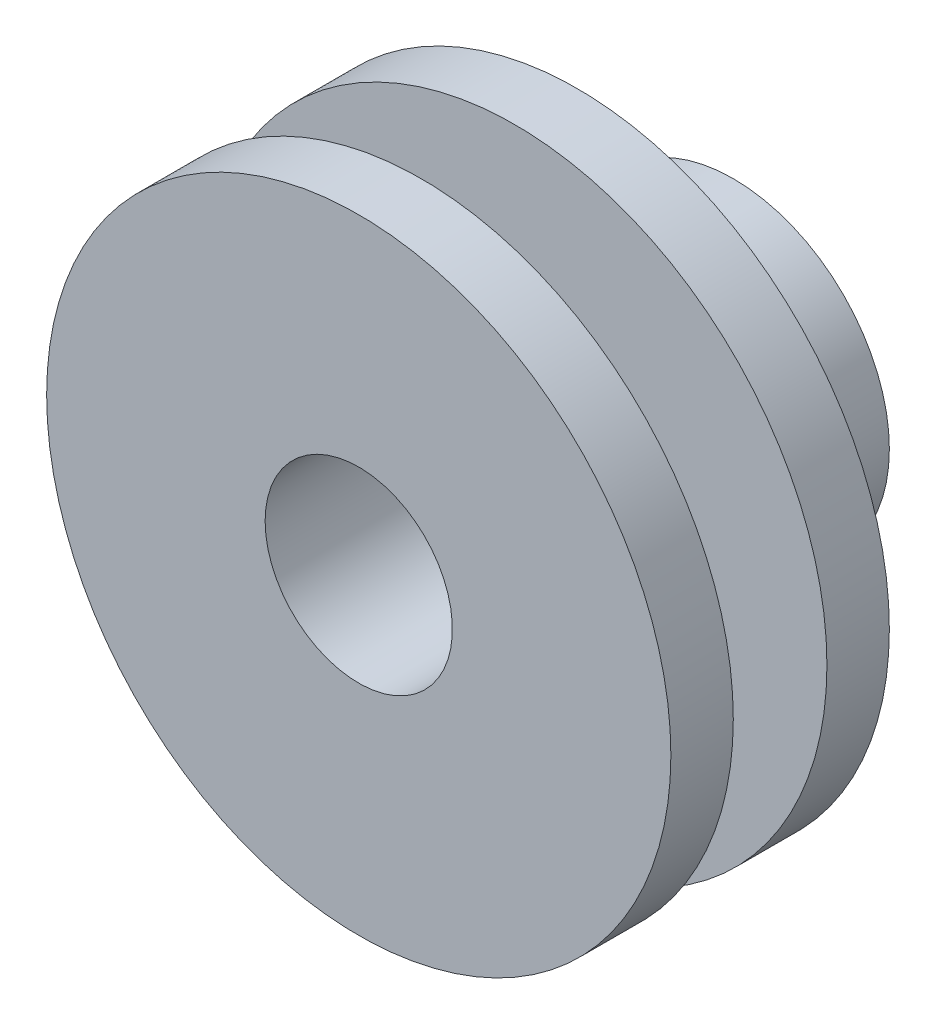
SolidWorks part; units mm, degrees
ref_plane "正面" through (0, 0, 0) normal (0, 0, 1) x (1, 0, 0)
ref_plane "平面" through (0, 0, 0) normal (0, 1, 0) x (1, 0, 0)
ref_plane "右側面" through (0, 0, 0) normal (1, 0, 0) x (0, 0, -1)
sketch "ｽｹｯﾁ1" plane through (0, 0, 0) normal (0, 0, 1) x (1, 0, 0)
  circle A0 centre (0, 0) radius 3
  circle A1 centre (0, 0) radius 5
  dimension "D1" = 6
  dimension "D2" = 10
extrude "ﾎﾞｽ - 押し出し1" add sketch "ｽｹｯﾁ1" along normal blind 5
sketch "ｽｹｯﾁ2" plane through (0, 0, 5) normal (0, 0, 1) x (1, 0, 0)
  circle A0 centre (0, 0) radius 3
  circle A1 centre (0, 0) radius 10
  dimension "D1" = 20
extrude "ﾎﾞｽ - 押し出し2" add sketch "ｽｹｯﾁ2" along normal blind 2
sketch "ｽｹｯﾁ3" plane through (0, 0, 7) normal (0, 0, 1) x (1, 0, 0)
  circle A0 centre (0, 0) radius 5
  dimension "D1" = 10
extrude "ﾎﾞｽ - 押し出し3" add sketch "ｽｹｯﾁ3" along normal blind 3
sketch "ｽｹｯﾁ4" plane through (0, 0, 10) normal (0, 0, 1) x (1, 0, 0)
  circle A0 centre (0, 0) radius 10
  dimension "D1" = 20
extrude "ﾎﾞｽ - 押し出し4" add sketch "ｽｹｯﾁ4" along normal blind 2
sketch "ｽｹｯﾁ5" plane through (0, 0, 7) normal (0, 0, -1) x (-1, 0, 0)
  circle A0 centre (0, 0) radius 3
extrude "ｶｯﾄ - 押し出し1" cut sketch "ｽｹｯﾁ5" against normal through all
hole_wizard "M3x0.5 ねじ穴1" positions "3Dｽｹｯﾁ1" profile "ｽｹｯﾁ6" tap size "M3x0.5" standard "JIS"
sketch3d "3Dｽｹｯﾁ1"
  point P0 (0.2512, -4.9937, 2.1439)
sketch "ｽｹｯﾁ6" plane through (0.2512, -4.9937, 2.1439) normal (0, 0, 1) x (0.9987, 0.0502, 0)
  line L0 (0, 0) -> (0, 2)
  line L1 (0, 2) -> (1.25, 2)
  line L2 (1.25, 2) -> (1.25, 0)
  line L5 (1.25, 0) -> (0, 0)
  line L11 (0, -6.35) -> (0, 107.95) construction
  dimension "次ｻｰﾌｪｽまでのねじ下穴ﾄﾞﾘﾙ直径" = 2.5
  dimension "次ｻｰﾌｪｽまでのねじ下穴ﾄﾞﾘﾙの深さ" = 2
cosmetic thread "穴のねじ山1" parameters "D2"=3
